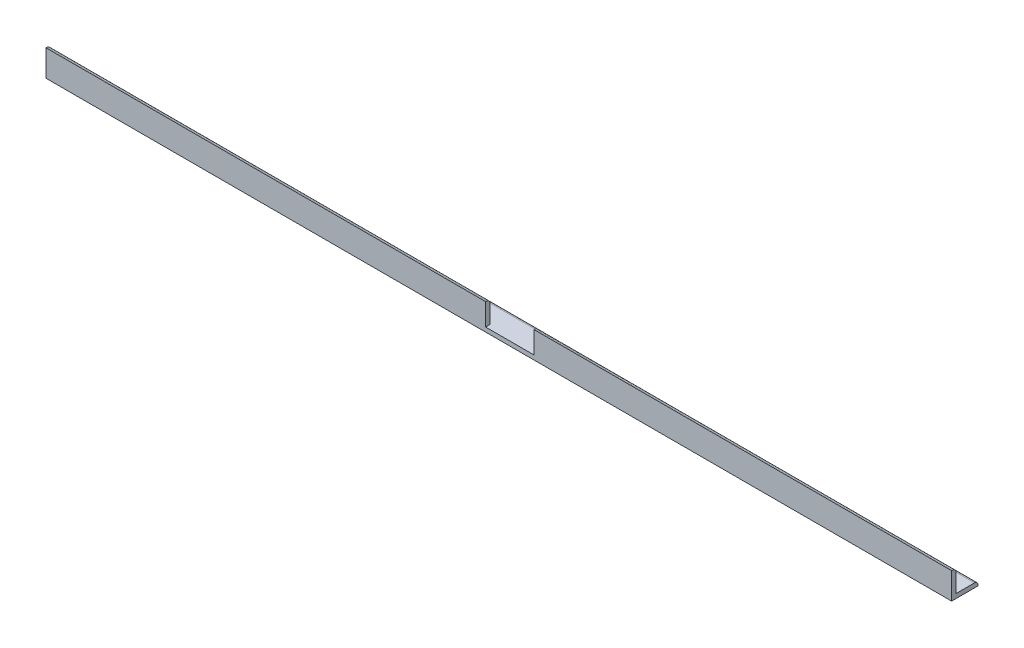
SolidWorks part; units mm, degrees
ref_plane "Front" through (0, 0, 0) normal (0, 0, 1) x (1, 0, 0)
ref_plane "Top" through (0, 0, 0) normal (0, 1, 0) x (1, 0, 0)
ref_plane "Right" through (0, 0, 0) normal (1, 0, 0) x (0, 0, -1)
sketch "Sketch1" plane through (0, 0, 0) normal (1, 0, 0) x (0, 0, -1)
  line L0 (3.175, 3.175) -> (16.51, 3.175)
  line L1 (0, 0) -> (19.05, 0)
  line L2 (0, 0) -> (0, 19.05)
  line L5 (3.175, 3.175) -> (3.175, 16.51)
  line L6 (19.05, 0) -> (19.05, 0.635)
  line L7 (0, 19.05) -> (0.635, 19.05)
  line L8 (3.175, 3.175) -> (3.175, 19.05) construction
  line L9 (3.175, 3.175) -> (19.05, 3.175) construction
  arc A0 (3.175, 16.51) -> (0.635, 19.05) centre (0.635, 16.51) ccw
  arc A1 (16.51, 3.175) -> (19.05, 0.635) centre (16.51, 0.635) cw
  dimension "D3" = 2.54
  dimension "D1" = 19.05
  dimension "D2" = 3.175
extrude "Boss-Extrude1" add sketch "Sketch1" along normal blind 654.0729
sketch "Sketch2" plane through (0, 3.175, 0) normal (0, 1, 0) x (1, 0, 0)
  line L0 (654.0729, 9.8425) -> (641.3729, 9.8425) construction
  line L1 (654.0729, 16.51) -> (654.0729, 3.175) construction
  line L2 (641.3729, 9.8425) -> (12.7, 9.8425) construction
  circle A0 centre (641.3729, 9.8425) radius 2.54
  circle A1 centre (12.7, 9.8425) radius 2.54
  dimension "D2" = 5.08
  dimension "D4" = 5.08
  dimension "D1" = 12.7
  dimension "D3" = 628.6729
extrude "Cut-Extrude1" cut sketch "Sketch2" against normal up to next
sketch "Sketch3" plane through (0, 0, -3.175) normal (0, 0, -1) x (-1, 0, 0)
  line L0 (-654.0729, 3.175) -> (0, 3.175) construction
  line L1 (-352.4479, 3.175) -> (-317.5229, 3.175)
  line L2 (-352.4479, 3.175) -> (-352.4479, 52.5176)
  line L3 (-352.4479, 52.5176) -> (-317.5229, 52.5176)
  line L4 (-317.5229, 3.175) -> (-317.5229, 52.5176)
  line L5 (-352.4479, 3.175) -> (-317.5229, 52.5176) construction
  line L6 (-352.4479, 52.5176) -> (-317.5229, 3.175) construction
  line L7 (-654.0729, 9.8425) -> (-352.4479, 9.8425) construction
  line L8 (-654.0729, 3.175) -> (-654.0729, 16.51) construction
  point P4 (-334.9854, 27.8463)
  dimension "D1" = 34.925
  dimension "D2" = 301.625
extrude "Cut-Extrude2" cut sketch "Sketch3" against normal through all
